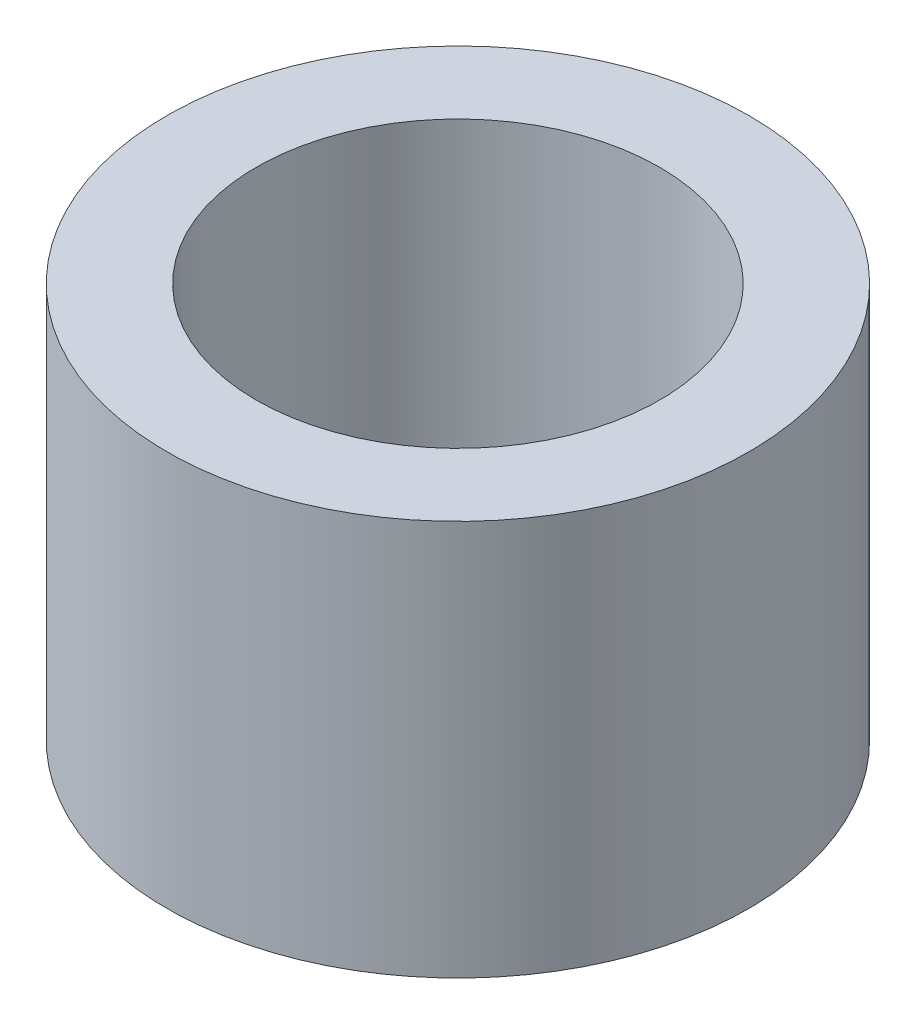
SolidWorks part; units mm, degrees
material "Nylon 6/10"
ref_plane "Front Plane" through (0, 0, 0) normal (0, 0, 1) x (1, 0, 0)
ref_plane "Top Plane" through (0, 0, 0) normal (0, 1, 0) x (1, 0, 0)
ref_plane "Right Plane" through (0, 0, 0) normal (1, 0, 0) x (0, 0, -1)
sketch "Sketch1" plane through (0, 0, 0) normal (0, 0, 1) x (1, 0, 0)
  line L0 (0, 0) -> (0, 29.6761) construction
  line L1 (-28.0416, 38.1) -> (-19.431, 38.1)
  line L2 (-28.0416, 38.1) -> (-28.0416, 0)
  line L3 (-28.0416, 0) -> (-19.431, 0)
  line L4 (-19.431, 38.1) -> (-19.431, 0)
  dimension "D1" = 0
  dimension "D2" = 19.431
  dimension "D3" = 28.0416
  dimension "D4" = 38.1
revolve "Revolve1" add sketch "Sketch1" angle 360 about L0
